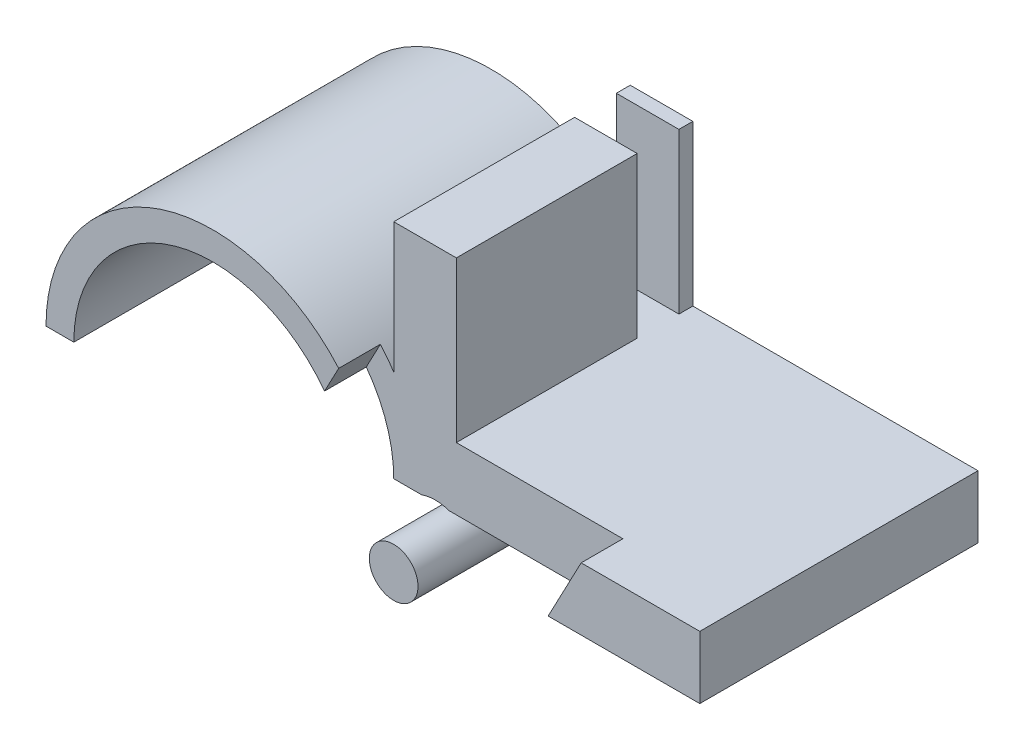
SolidWorks part; units mm, degrees
ref_plane "Front Plane" through (0, 0, 0) normal (0, 0, 1) x (1, 0, 0)
ref_plane "Top Plane" through (0, 0, 0) normal (0, 1, 0) x (1, 0, 0)
ref_plane "Right Plane" through (0, 0, 0) normal (1, 0, 0) x (0, 0, -1)
sketch "Sketch1" plane through (0, 0, 0) normal (0, 0, 1) x (1, 0, 0)
  line L9 (-10, 0) -> (-12, 0)
  line L10 (12, 0) -> (10, 0)
  arc A7 (11.8333, 1.993) -> (-12, 0) centre (0, 0) ccw
  arc A8 (10, 0) -> (-10, 0) centre (0, 0) ccw
  arc A13 (11.94, 1.1985) -> (-12, 0) centre (0, 0) ccw
  arc A15 (11.94, 1.1985) -> (12, 0) centre (0, 0) cw
  dimension "D1" = 24
  dimension "D2" = 20
extrude "Boss-Extrude1" add sketch "Sketch1" along normal blind 20
ref_plane "Plane1" through (-12, 0, 0) normal (-1, 0, 0) x (0, 0, -1)
sketch "Sketch5" plane through (0, 0, 0) normal (0, 0, -1) x (-1, 0, 0)
  line L0 (-10, 0) -> (-10, -2.6091)
  line L1 (-10, 0) -> (-12, 0)
  arc A0 (-12, 0) -> (-10, -2.6091) centre (-12.9918, -2.8313) ccw
  dimension "D2" = 3
sketch "Sketch7" plane through (0, 0, 0) normal (0, 0, -1) x (-1, 0, 0)
  circle A0 centre (-12.9918, -2.8313) radius 1.75
  dimension "D1" = 3.5
extrude "Boss-Extrude5" add sketch "Sketch7" against normal blind 20 separate body
extrude "Boss-Extrude6" add sketch "Sketch5" against normal blind 5
sketch "Sketch8" plane through (0, 0, 0) normal (0, 1, 0) x (1, 0, 0)
  line L5 (10, -20) -> (35, -20)
  line L6 (10, -20) -> (10, 0)
  line L7 (10, 0) -> (35, 0)
  line L8 (35, -20) -> (35, 0)
  dimension "D1" = 25
  dimension "D2" = 20
extrude "Boss-Extrude7" add sketch "Sketch8" along normal blind 4.5
sketch "Sketch9" plane through (0, 0, 0) normal (0, -1, 0) x (1, 0, 0)
  line L0 (35, 0) -> (13.9835, 0) construction
  line L1 (10, 20) -> (14.5, 20)
  line L2 (10, 20) -> (10, 0)
  line L3 (10, 0) -> (14.5, 0)
  line L4 (14.5, 20) -> (14.5, 0)
  dimension "D1" = 4.5
extrude "Boss-Extrude8" add sketch "Sketch9" against normal blind 16
sketch "Sketch10" plane through (0, 0, 20) normal (0, 0, 1) x (1, 0, 0)
  line L0 (14.5, 16) -> (14.5, 4.5) construction
  line L1 (14.5, 4.5) -> (35, 4.5) construction
  line L2 (19.5, 9.5) -> (12.9918, -2.8313) construction
  line L3 (19.5, 9.5) -> (12.9918, -2.8313) construction
  line L4 (27.0173, 5.5325) -> (20.509, -6.7988)
  line L5 (11.9827, 13.4675) -> (5.4745, 1.1361)
  circle A0 centre (19.5, 9.5) radius 8
  circle A1 centre (12.9918, -2.8313) radius 8
  arc A2 (27.0173, 5.5325) -> (11.9827, 13.4675) centre (19.5, 9.5) ccw
  arc A3 (5.4745, 1.1361) -> (20.509, -6.7988) centre (12.9918, -2.8313) ccw
  circle A4 centre (12.9918, -2.8313) radius 6
  circle A5 centre (19.5, 9.5) radius 6
  point P10 (16.2459, 3.3343)
  line M8 (35, 4.5) -> (14.5, 4.5)
  line M9 (14.5, 4.5) -> (14.5, 16)
  dimension "D3" = 16
  dimension "D4" = 16
  dimension "D5" = 8.5
  dimension "D6" = 12
  dimension "D7" = 12
  dimension "D1" = 5
  dimension "D2" = 5
extrude "Cut-Extrude1" cut sketch "Sketch10" against normal blind 3 contours L4 A2 A0 M9 M8
sketch "Sketch11" plane through (0, 0, 17) normal (0, 0, 1) x (1, 0, 0)
  line L0 (26.4723, 4.5) -> (14.5, 4.5) construction
  line L1 (14.5, 16) -> (14.5, 4.5) construction
  point P0 (19.5, 9.5)
  dimension "D1" = 5
  dimension "D2" = 5
sketch "Sketch12" plane through (0, 0, 17) normal (0, 0, 1) x (1, 0, 0)
  circle A0 centre (12.9918, -2.8313) radius 1.75
extrude "Boss-Extrude9" add sketch "Sketch12" along normal blind 3
sketch "Sketch14" plane through (0, 0, 5) normal (0, 0, 1) x (1, 0, 0)
  circle A0 centre (12.9918, -2.8313) radius 3
  circle A1 centre (12.9918, -2.8313) radius 2.3339
extrude "Cut-Extrude3" cut sketch "Sketch14" along normal blind 16
sketch "Sketch15" plane through (0, 0, 20) normal (0, 0, 1) x (1, 0, 0)
  line L0 (9.3321, 17.0117) -> (15.8357, 16.7616)
  line L1 (15.8357, 16.7616) -> (11.7223, 9.2852)
  line L2 (11.7223, 9.2852) -> (9.051, 9.7012)
  line L3 (9.051, 9.7012) -> (9.3321, 17.0117)
extrude "Cut-Extrude4" cut sketch "Sketch15" against normal up to surface (3 mm away) up to face at (13.7694, 6.5471, 17)
sketch "Sketch16" plane through (14.5, 0, 0) normal (1, 0, 0) x (0, 0, -1)
  line L0 (0, 16) -> (-17, 16) construction
  line L1 (-4, 16) -> (-1, 16)
  line L2 (-4, 16) -> (-4, 4.5)
  line L3 (-4, 4.5) -> (-1, 4.5)
  line L4 (-1, 16) -> (-1, 4.5)
  line L5 (-17, 16) -> (-17, 4.5) construction
  dimension "D1" = 13
  dimension "D2" = 3
  dimension "D3" = 11.5
extrude "Cut-Extrude5" cut sketch "Sketch16" against normal blind 5
